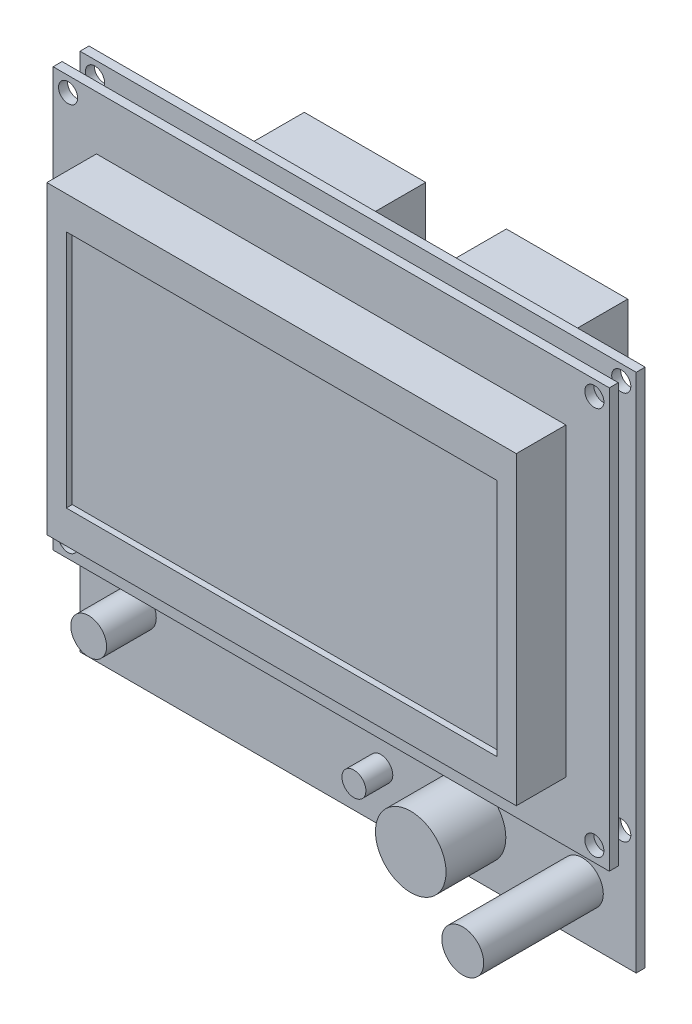
SolidWorks part; units mm, degrees
ref_plane "Plano frontal" through (0, 0, 0) normal (0, 0, 1) x (1, 0, 0)
ref_plane "Plano superior" through (0, 0, 0) normal (0, 1, 0) x (1, 0, 0)
ref_plane "Plano direito" through (0, 0, 0) normal (1, 0, 0) x (0, 0, -1)
sketch "Esboço1" plane through (0, 0, 0) normal (0, 0, 1) x (1, 0, 0)
  line L1 (-46.5, 43.5) -> (46.5, 43.5)
  line L2 (-46.5, 43.5) -> (-46.5, -43.5)
  line L3 (-46.5, -43.5) -> (46.5, -43.5)
  line L4 (46.5, 43.5) -> (46.5, -43.5)
  line L5 (-46.5, 43.5) -> (46.5, -43.5) construction
  line L6 (-46.5, -43.5) -> (46.5, 43.5) construction
  point P0 (0, 0)
  dimension "D1" = 93
  dimension "D2" = 87
extrude "Ressalto-extrusão1" add sketch "Esboço1" along normal blind 1.5
sketch "Esboço3" plane through (0, 0, 1.5) normal (0, 0, 1) x (1, 0, 0)
  line L0 (46.5, -43.5) -> (46.5, 43.5) construction
  line L1 (-46.5, 43.5) -> (46.5, 43.5)
  line L2 (-46.5, 43.5) -> (-46.5, -26.5)
  line L3 (-46.5, -26.5) -> (46.5, -26.5)
  line L4 (46.5, 43.5) -> (46.5, -26.5)
  line L5 (-46.5, 43.5) -> (46.5, -26.5) construction
  line L6 (-46.5, -26.5) -> (46.5, 43.5) construction
  line L7 (-46.5, 43.5) -> (-46.5, -43.5) construction
  line L8 (46.5, 43.5) -> (-46.5, 43.5) construction
  point P0 (0, 8.5)
  dimension "D1" = 70
extrude "Ressalto-extrusão2" add sketch "Esboço3" along normal blind 1.5 from offset 3 separate body
sketch "Esboço4" plane through (0, 0, 6) normal (0, 0, 1) x (1, 0, 0)
  line L0 (46.5, 43.5) -> (-46.5, 43.5) construction
  line L1 (-39.25, 34.5) -> (39.25, 34.5)
  line L2 (-39.25, 34.5) -> (-39.25, -16.5)
  line L3 (-39.25, -16.5) -> (39.25, -16.5)
  line L4 (39.25, 34.5) -> (39.25, -16.5)
  line L5 (-39.25, 34.5) -> (39.25, -16.5) construction
  line L6 (-39.25, -16.5) -> (39.25, 34.5) construction
  point P0 (0, 9)
  dimension "D1" = 51
  dimension "D2" = 78.5
  dimension "D3" = 9
extrude "Ressalto-extrusão3" add sketch "Esboço4" along normal blind 8.3
sketch "Esboço5" plane through (0, 0, 14.3) normal (0, 0, 1) x (1, 0, 0)
  line L0 (39.25, -16.5) -> (39.25, 34.5) construction
  line L1 (-36, 29) -> (36, 29)
  line L2 (-36, 29) -> (-36, -11)
  line L3 (-36, -11) -> (36, -11)
  line L4 (36, 29) -> (36, -11)
  line L5 (-36, 29) -> (36, -11) construction
  line L6 (-36, -11) -> (36, 29) construction
  line L7 (39.25, 34.5) -> (-39.25, 34.5) construction
  point P0 (0, 9)
  point P7 (39.25, 9)
  point P11 (0, 34.5)
  dimension "D1" = 72
  dimension "D2" = 40
extrude "Corte-extrusão1" cut sketch "Esboço5" against normal blind 1
sketch "Esboço6" plane through (0, 0, 1.5) normal (0, 0, 1) x (1, 0, 0)
  line L0 (46.5, -43.5) -> (46.5, 43.5) construction
  line L1 (-46.5, -43.5) -> (46.5, -43.5) construction
  circle A0 centre (37.5, -34.8) radius 3.5
  dimension "D3" = 7
  dimension "D1" = 9
  dimension "D2" = 8.7
extrude "Ressalto-extrusão4" add sketch "Esboço6" along normal blind 20
sketch "Esboço7" plane through (0, 0, 1.5) normal (0, 0, 1) x (1, 0, 0)
  line L0 (46.5, -43.5) -> (46.5, 43.5) construction
  line L1 (-46.5, -43.5) -> (46.5, -43.5) construction
  circle A0 centre (3.8, -35.2) radius 2
  dimension "D3" = 4
  dimension "D1" = 42.7
  dimension "D2" = 8.3
extrude "Ressalto-extrusão5" add sketch "Esboço7" along normal blind 4.5
sketch "Esboço8" plane through (0, 0, 1.5) normal (0, 0, 1) x (1, 0, 0)
  line L0 (-46.5, -43.5) -> (46.5, -43.5) construction
  line L1 (46.5, -43.5) -> (46.5, 43.5) construction
  circle A0 centre (18.8, -34.8) radius 5.9
  dimension "D3" = 11.8
  dimension "D1" = 8.7
  dimension "D2" = 27.7
extrude "Ressalto-extrusão6" add sketch "Esboço8" along normal blind 10
sketch "Esboço9" plane through (0, 0, 1.5) normal (0, 0, 1) x (1, 0, 0)
  line L0 (-46.5, 43.5) -> (-46.5, -43.5) construction
  line L1 (-46.5, -43.5) -> (46.5, -43.5) construction
  circle A0 centre (-36.75, -32.2) radius 3
  dimension "D3" = 6
  dimension "D1" = 9.75
  dimension "D2" = 11.3
extrude "Ressalto-extrusão7" add sketch "Esboço9" along normal blind 8.3
sketch "Esboço10" plane through (0, 0, 6) normal (0, 0, 1) x (1, 0, 0)
  line L0 (46.5, 43.5) -> (-46.5, 43.5) construction
  line L1 (0, 0) -> (0, 41) construction
  circle A0 centre (-44, 41) radius 1.6
  circle A1 centre (44, 41) radius 1.6
  circle A2 centre (44, -24) radius 1.6
  circle A3 centre (-44, -24) radius 1.6
  dimension "D1" = 3.2
  dimension "D2" = 2.5
  dimension "D3" = 88
  dimension "D4" = 65
extrude "Corte-extrusão2" cut sketch "Esboço10" against normal through all both and the other way through all
sketch "Esboço11" plane through (0, 0, 0) normal (0, 0, -1) x (-1, 0, 0)
  line L0 (-46.5, 43.5) -> (46.5, 43.5) construction
  line L1 (-28.5887, 36.9) -> (-8.2887, 36.9)
  line L2 (-28.5887, 36.9) -> (-28.5887, 28.3)
  line L3 (-28.5887, 28.3) -> (-8.2887, 28.3)
  line L4 (-8.2887, 36.9) -> (-8.2887, 28.3)
  line L5 (-28.5887, 36.9) -> (-8.2887, 28.3) construction
  line L6 (-28.5887, 28.3) -> (-8.2887, 36.9) construction
  line L7 (5.2, 36.9) -> (25.5, 36.9)
  line L8 (5.2, 36.9) -> (5.2, 28.3)
  line L9 (5.2, 28.3) -> (25.5, 28.3)
  line L10 (25.5, 36.9) -> (25.5, 28.3)
  line L11 (5.2, 36.9) -> (25.5, 28.3) construction
  line L12 (5.2, 28.3) -> (25.5, 36.9) construction
  line L13 (46.5, 43.5) -> (46.5, -43.5) construction
  point P0 (-18.4387, 32.6)
  point P5 (15.35, 32.6)
  dimension "D1" = 13.4887
  dimension "D2" = 6.6
  dimension "D3" = 20.3
  dimension "D4" = 21
  dimension "D5" = 8.6
extrude "Ressalto-extrusão8" add sketch "Esboço11" along normal blind 15
sketch "Esboço12" plane through (0, 0, 0) normal (0, 0, -1) x (-1, 0, 0)
  line L0 (46.5, 43.5) -> (46.5, -43.5) construction
  line L1 (46.4, 21.5) -> (20.9, 21.5)
  line L2 (46.4, 21.5) -> (46.4, -5)
  line L3 (46.4, -5) -> (20.9, -5)
  line L4 (20.9, 21.5) -> (20.9, -5)
  line L5 (-46.5, 43.5) -> (46.5, 43.5) construction
  dimension "D1" = 26.5
  dimension "D2" = 25.5
  dimension "D3" = 0.1
  dimension "D4" = 22
extrude "Ressalto-extrusão9" add sketch "Esboço12" along normal blind 3
